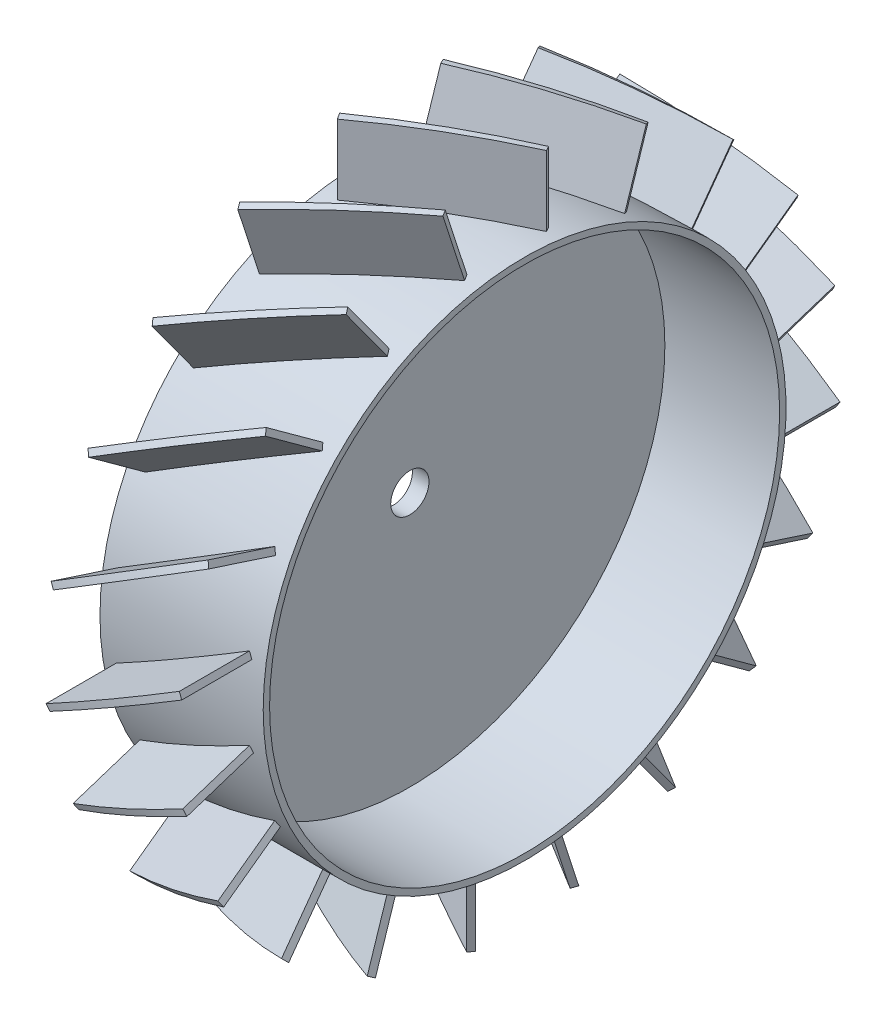
SolidWorks part; units mm, degrees
ref_plane "Front Plane" through (0, 0, 0) normal (0, 0, 1) x (1, 0, 0)
ref_plane "Top Plane" through (0, 0, 0) normal (0, 1, 0) x (1, 0, 0)
ref_plane "Right Plane" through (0, 0, 0) normal (1, 0, 0) x (0, 0, -1)
sketch "Sketch1" plane through (0, 0, 0) normal (0, 1, 0) x (1, 0, 0)
  line L0 (3.302, 0) -> (3.302, 50.8)
  line L1 (3.302, 50.8) -> (26.162, 50.8)
  line L2 (26.162, 50.8) -> (26.162, 52.07)
  line L3 (26.162, 52.07) -> (-6.35, 52.07)
  line L4 (-6.35, 52.07) -> (-6.35, 50.8)
  line L5 (-6.35, 50.8) -> (0, 50.8)
  line L6 (0, 50.8) -> (0, 0)
  line L7 (0, 0) -> (3.302, 0)
  dimension "D1" = 3.302
  dimension "D2" = 1.27
  dimension "D3" = 50.8
  dimension "D4" = 32.512
  dimension "D5" = 6.35
revolve "Revolve1" add sketch "Sketch1" angle 360 about L7
ref_plane "Plane1" through (0, 0, 83.82) normal (0, 0, 1) x (1, 0, 0)
sketch "Sketch2" plane through (0, 0, 83.82) normal (0, 0, 1) x (1, 0, 0)
  line L0 (-2.9747, -8.1699) -> (23.4217, 7.0701)
  line L1 (23.4217, 7.0701) -> (22.7867, 8.1699)
  line L3 (22.7867, 8.1699) -> (-3.6097, -7.0701)
  line L4 (-3.6097, -7.0701) -> (-2.9747, -8.1699)
  line L5 (-6.35, 0) -> (26.162, 0) construction
  line L6 (-6.35, 52.07) -> (-6.35, -52.07) construction
  line L7 (26.162, -52.07) -> (26.162, 52.07) construction
  line L8 (10.2235, -0.5499) -> (9.5885, 0.5499) construction
  point P4 (9.906, 0)
  point P13 (9.906, 0)
  dimension "D1" = 1.27
  dimension "D2" = 30
  dimension "D3" = 30.48
extrude "Boss-Extrude1" add sketch "Sketch2" along normal blind 13.97 from surface starting at face at (-6.35, 0, 52.07)
pattern_circular "CirPattern15" count 20 over 360 about axis through (0, 0, 0) along (1, 0, 0) of "Boss-Extrude1"
sketch "Sketch7" plane through (0, 0, 0) normal (-1, 0, 0) x (0, 0, 1)
  circle A0 centre (0, 0) radius 3.81
  dimension "D1" = 7.62
extrude "Cut-Extrude1" cut sketch "Sketch7" against normal through all
